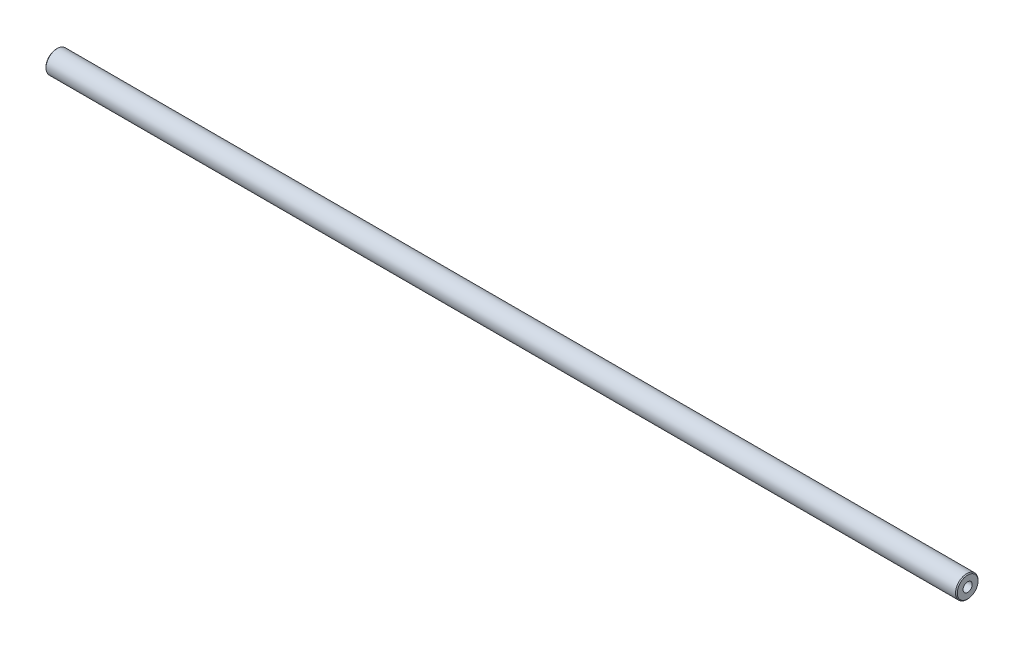
SolidWorks part; units mm, degrees
material "Plain Carbon Steel"
ref_plane "Front Plane" through (0, 0, 0) normal (0, 0, 1) x (1, 0, 0)
ref_plane "Top Plane" through (0, 0, 0) normal (0, 1, 0) x (1, 0, 0)
ref_plane "Right Plane" through (0, 0, 0) normal (1, 0, 0) x (0, 0, -1)
sketch "Sketch1" plane through (0, 0, 0) normal (0, 1, 0) x (1, 0, 0)
  line L0 (-267.3058, 0) -> (267.3058, 0) construction
  line L1 (-257, 6.35) -> (257, 6.35)
  line L2 (257, 6.35) -> (257, 2.6)
  line L3 (257, 2.6) -> (235.2011, 2.6)
  line L4 (235.2011, 2.6) -> (233.7, 0)
  line L5 (233.7, 0) -> (-233.7, 0)
  line L6 (-233.7, 0) -> (-235.2011, 2.6)
  line L7 (-235.2011, 2.6) -> (-257, 2.6)
  line L8 (-257, 2.6) -> (-257, 6.35)
  line L9 (0, 0) -> (0, 65.3829) construction
  dimension "D1" = 60
  dimension "D2" = 60
  dimension "D3" = 12.7
  dimension "D4" = 5.2
  dimension "D5" = 514
  dimension "D6" = 23.3
revolve "Revolve1" add sketch "Sketch1" angle 360 about L0
chamfer "Chamfer1" distance 0.5 angle 45 2 edges at (257, 0, 6.35) (-257, 0, 6.35)
